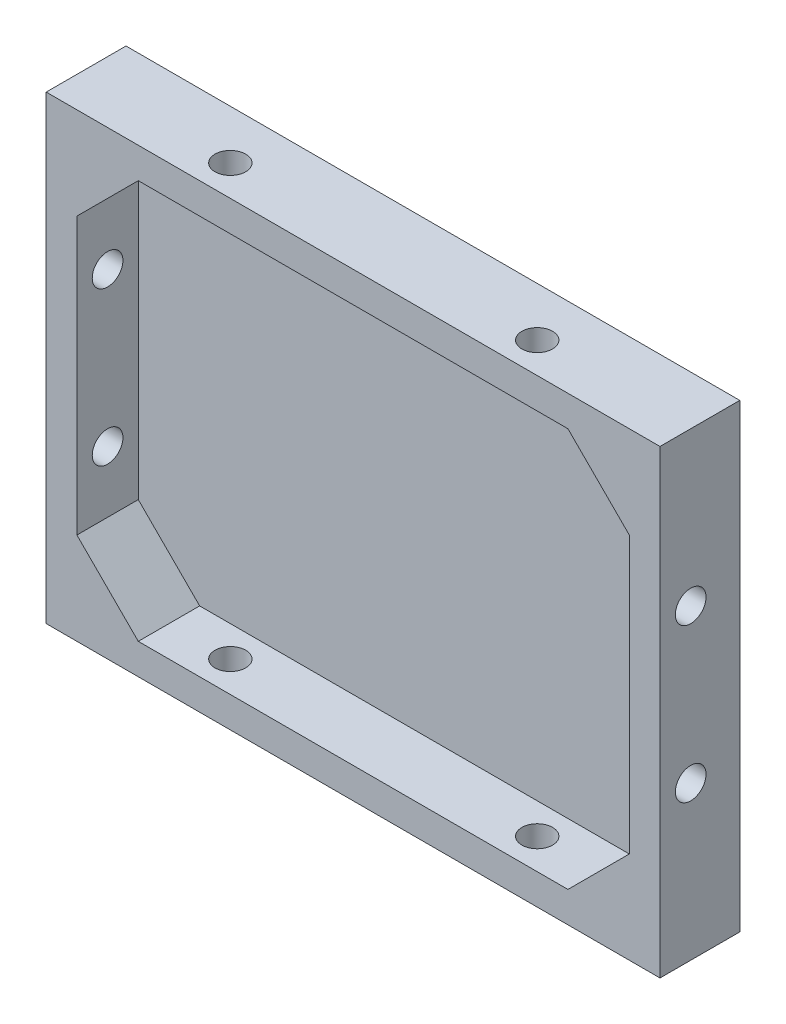
SolidWorks part; units mm, degrees
ref_plane "Plan de face" through (0, 0, 0) normal (0, 0, 1) x (1, 0, 0)
ref_plane "Plan de dessus" through (0, 0, 0) normal (0, 1, 0) x (1, 0, 0)
ref_plane "Plan de droite" through (0, 0, 0) normal (1, 0, 0) x (0, 0, -1)
sketch "Esquisse1" plane through (0, 0, 0) normal (0, 0, 1) x (1, 0, 0)
  line L0 (44.1184, 33.7284) -> (54.1184, 33.7284)
  line L1 (-45.8816, 33.7284) -> (44.1184, 33.7284)
  line L2 (-45.8816, 33.7284) -> (-45.8816, -41.2716)
  line L3 (-45.8816, -41.2716) -> (54.1184, -41.2716)
  line L4 (54.1184, 23.7284) -> (54.1184, -41.2716)
  line L5 (54.1184, 33.7284) -> (54.1184, 23.7284)
  point P6 (54.1184, 33.7284)
  dimension "D1" = 100
  dimension "D2" = 75
extrude "Boss.-Extru.1" add sketch "Esquisse1" along normal blind 13
shell "Coque1" thickness 5
sketch "Esquisse2" plane through (-45.8816, 0, 0) normal (-1, 0, 0) x (0, 0, 1)
  line L0 (13, 33.7284) -> (13, -41.2716) construction
  line L1 (13, 33.7284) -> (0, 33.7284) construction
  line L2 (13, -41.2716) -> (0, -41.2716) construction
  circle A0 centre (8, 8.7284) radius 2.5
  circle A1 centre (8, -16.2716) radius 2.5
  dimension "D1" = 5
  dimension "D2" = 5
  dimension "D3" = 5
  dimension "D4" = 5
  dimension "D5" = 25
  dimension "D6" = 25
extrude "Enlèv. mat.-Extru.1" cut sketch "Esquisse2" against normal up to surface (100 mm away) contours A1 | A0 up to face at (54.1184, -3.7716, 6.5)
sketch "Esquisse3" plane through (0, -41.2716, 0) normal (0, -1, 0) x (1, 0, 0)
  line L0 (-45.8816, 13) -> (54.1184, 13) construction
  line L2 (54.1184, 13) -> (54.1184, 0) construction
  line L3 (-45.8816, 13) -> (-45.8816, 0) construction
  circle A0 centre (-20.8816, 8) radius 2.5
  circle A1 centre (29.1184, 8) radius 2.5
  dimension "D1" = 5
  dimension "D2" = 5
  dimension "D3" = 5
  dimension "D4" = 5
  dimension "D5" = 25
  dimension "D6" = 25
extrude "Enlèv. mat.-Extru.2" cut sketch "Esquisse3" against normal up to surface (75 mm away) up to face at (4.1184, 33.7284, 6.5)
sketch "Esquisse4" plane through (0, 0, 3) normal (0, 0, 1) x (1, 0, 0)
  line L0 (-30.8816, 28.7284) -> (-40.8816, 18.7284)
  line L1 (49.1184, 28.7284) -> (-40.8816, 28.7284) construction
  line L2 (-40.8816, 28.7284) -> (-40.8816, -36.2716) construction
  line L3 (-40.8816, 18.7284) -> (-40.8816, 28.7284)
  line L4 (-40.8816, 28.7284) -> (-30.8816, 28.7284)
  line L5 (49.1184, 28.7284) -> (49.1184, 18.7284)
  line L6 (49.1184, -36.2716) -> (49.1184, 28.7284) construction
  line L7 (49.1184, 18.7284) -> (39.1184, 28.7284)
  line L8 (39.1184, 28.7284) -> (49.1184, 28.7284)
  line L9 (49.1184, 28.7284) -> (-40.8816, 28.7284) construction
  line L10 (49.1184, -36.2716) -> (49.1184, -26.2716)
  line L11 (49.1184, -26.2716) -> (39.1184, -36.2716)
  line L12 (-40.8816, -36.2716) -> (49.1184, -36.2716) construction
  line L13 (39.1184, -36.2716) -> (49.1184, -36.2716)
  line L14 (-30.8816, -36.2716) -> (-40.8816, -26.2716)
  line L15 (-40.8816, 28.7284) -> (-40.8816, -36.2716) construction
  line L16 (-40.8816, -26.2716) -> (-40.8816, -36.2716)
  line L17 (-40.8816, -36.2716) -> (-30.8816, -36.2716)
  dimension "D1" = 10
  dimension "D2" = 10
  dimension "D3" = 10
  dimension "D4" = 10
  dimension "D5" = 10
  dimension "D6" = 10
  dimension "D7" = 10
  dimension "D8" = 10
extrude "Boss.-Extru.2" add sketch "Esquisse4" along normal up to surface (10 mm away) up to face at (4.1184, -3.7716, 13)
